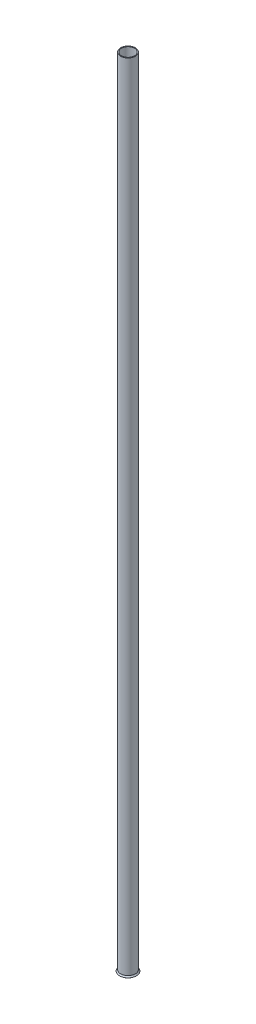
SolidWorks part; units mm, degrees
material "6061-T6 (SS)"
ref_plane "Front Plane" through (0, 0, 0) normal (0, 0, 1) x (1, 0, 0)
ref_plane "Top Plane" through (0, 0, 0) normal (0, 1, 0) x (1, 0, 0)
ref_plane "Right Plane" through (0, 0, 0) normal (1, 0, 0) x (0, 0, -1)
sketch "Sketch1" plane through (0, 0, 0) normal (0, 1, 0) x (1, 0, 0)
  circle A0 centre (0, 0) radius 25.4
  circle A1 centre (0, 0) radius 28.575
  dimension "D1" = 50.8
  dimension "D2" = 57.15
extrude "Boss-Extrude1" add sketch "Sketch1" along normal blind 3085.846
ref_axis "Axis1" through (0, -154.2923, 0) along (0, 1, 0)
sketch "Sketch3" plane through (0, 0, 0) normal (0, 0, 1) x (1, 0, 0)
  line L0 (28.575, 0) -> (32.6567, -4.8644)
  line L1 (-28.575, 0) -> (28.575, 0) construction
  line L2 (25.4, 0) -> (30.7935, -6.4278)
  line L3 (-25.4, 0) -> (25.4, 0) construction
  line L4 (28.575, 0) -> (33.2952, 0) construction
  line L5 (32.6567, -4.8644) -> (30.7935, -6.4278)
  line L6 (28.575, 0) -> (25.4, 0)
  dimension "D1" = 50
  dimension "D2" = 6.35
  dimension "D3" = 2.4322
  dimension "D4" = 25.4
revolve "Revolve1" add sketch "Sketch3" angle 360 about axis through (0, -154.2923, 0) along (0, 1, 0)
